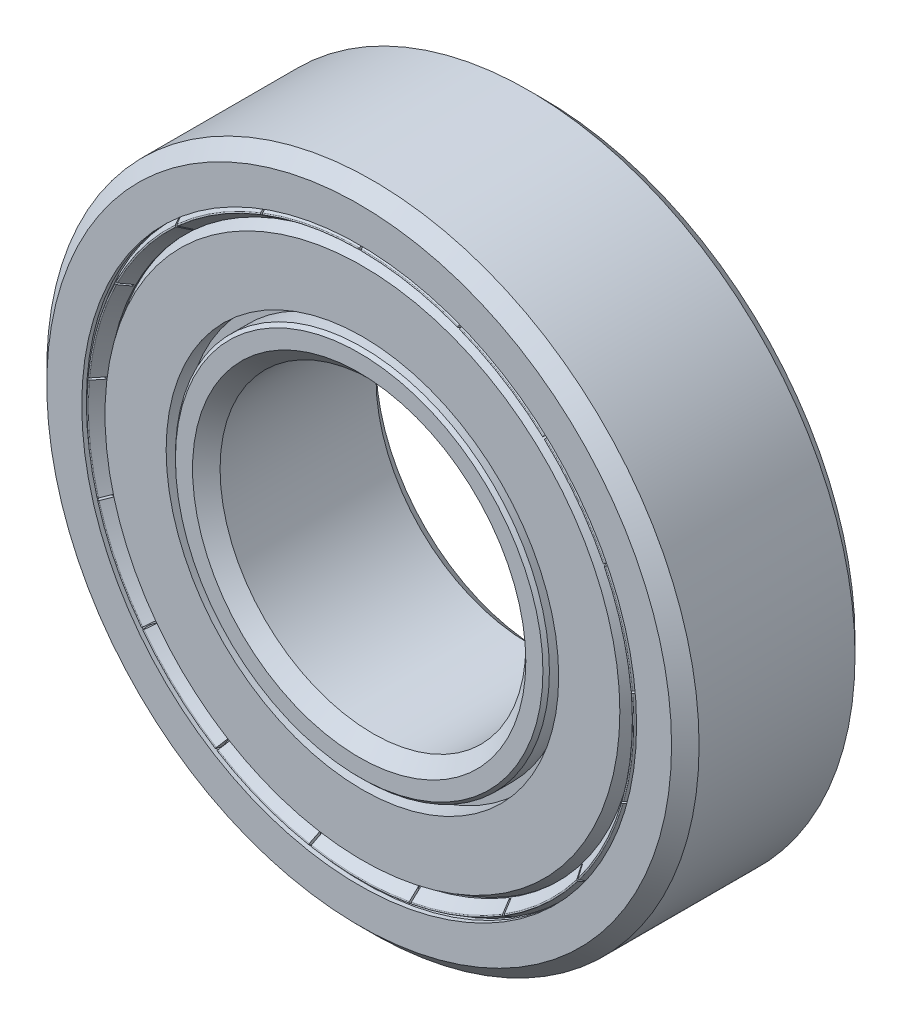
SolidWorks part; units mm, degrees
material "Plain Carbon Steel"
ref_plane "Front Plane" through (0, 0, 0) normal (0, 0, 1) x (1, 0, 0)
ref_plane "Top Plane" through (0, 0, 0) normal (0, 1, 0) x (1, 0, 0)
ref_plane "Right Plane" through (0, 0, 0) normal (1, 0, 0) x (0, 0, -1)
sketch "Sketch1" plane through (0, 0, 0) normal (0, 0, 1) x (1, 0, 0)
  circle A0 centre (0, 0) radius 7.5
  circle A1 centre (0, 0) radius 16
  dimension "OD" = 32
  dimension "ID" = 15
sketch "Sketch2" plane through (0, 0, 0) normal (1, 0, 0) x (0, 0, -1)
  line L0 (-4.5, 16) -> (4.5, 16)
  line L1 (-4.5, 7.5) -> (-4.5, -7.5) construction
  line L2 (4.5, 16) -> (4.5, -16) construction
  line L3 (-4.5, 0) -> (4.5, 0) construction
  line L6 (0, 16) -> (0, 7.5) construction
  circle A0 centre (0, 11.75) radius 2.975 construction
  point P8 (0, 16)
  dimension "Approx. Ball Dia." = 5.95
  dimension "Width" = 9
  dimension "For Shaft Diameter" = 15
  dimension "For Housing ID" = 32
sketch "Sketch3" plane through (0, 0, 0) normal (1, 0, 0) x (0, 0, -1)
  line L0 (0, 0) -> (0, 15) construction
  line L1 (-4.5, 7.5) -> (-4.5, -7.5) construction
  line L2 (3.825, 16) -> (-3.825, 16)
  line L3 (-3.825, 16) -> (-4.5, 15.325)
  line L4 (-4.5, 15.325) -> (-4.5, 13.6097)
  line L5 (-4.5, 13.6097) -> (-4.275, 13.6097)
  line L6 (-4.275, 13.6097) -> (-4.275, 14.1673)
  line L7 (-4.275, 14.1673) -> (-4.1159, 14.3264)
  line L8 (-4.1159, 14.3264) -> (-1.4875, 14.3264)
  line L10 (-4.5, 16) -> (4.5, 16) construction
  line L12 (-4.275, 14.1673) -> (-4.275, 14.725) construction
  line L13 (4.1159, 14.3264) -> (1.4875, 14.3264)
  line L14 (4.275, 14.1673) -> (4.1159, 14.3264)
  line L15 (4.275, 13.6097) -> (4.275, 14.1673)
  line L16 (4.5, 13.6097) -> (4.275, 13.6097)
  line L17 (4.5, 15.325) -> (4.5, 13.6097)
  line L18 (3.825, 16) -> (4.5, 15.325)
  line L19 (3.825, 7.5) -> (-3.825, 7.5)
  line L20 (-3.825, 7.5) -> (-4.5, 8.175)
  line L21 (-4.5, 8.175) -> (-4.5, 9.0145)
  line L22 (-4.5, 9.0145) -> (-4.3409, 9.1736)
  line L23 (-4.3409, 9.1736) -> (-1.4875, 9.1736)
  line L25 (4.3409, 9.1736) -> (1.4875, 9.1736)
  line L26 (4.5, 9.0145) -> (4.3409, 9.1736)
  line L27 (4.5, 8.175) -> (4.5, 9.0145)
  line L28 (3.825, 7.5) -> (4.5, 8.175)
  circle A2 centre (0, 11.75) radius 2.975 construction
  arc A3 (-1.4875, 14.3264) -> (1.4875, 14.3264) centre (0, 11.75) cw
  arc A4 (-1.4875, 9.1736) -> (1.4875, 9.1736) centre (0, 11.75) ccw
  point P5 (0, 14.725)
  point P31 (0, 16)
  point P37 (0, 7.5)
  dimension "D1" = 45
  dimension "D2" = 0.225
  dimension "D3" = 2.975
  dimension "D4" = 0.675
revolve "Revolve1" add sketch "Sketch3" angle 360 about L3
sketch "Sketch4" plane through (0, 0, 0) normal (1, 0, 0) x (0, 0, -1)
  line L0 (0, 14.725) -> (0, 8.775)
  line L1 (0, 16) -> (0, 7.5) construction
  circle A0 centre (0, 11.75) radius 2.975 construction
  arc A1 (0, 8.775) -> (0, 14.725) centre (0, 11.75) cw
revolve "Revolve2" add sketch "Sketch4" angle 360 about L6
pattern_circular "CirPattern1" count 8 over 360 about axis through (0, 0, 0) along (0, 0, 1) of bodies 106
sketch "Sketch5" plane through (0, 0, 0) normal (1, 0, 0) x (0, 0, -1)
  line L0 (-2.975, 11.75) -> (-2.975, 9.1736) construction
  line L1 (-4.3409, 9.1736) -> (-1.4875, 9.1736) construction
  line L3 (-2.975, 9.1736) -> (-3.4303, 9.1736)
  line L4 (-3.4303, 9.1736) -> (-3.4303, 9.6289)
  line L5 (-3.4303, 9.6289) -> (-4.3409, 9.6289)
  line L6 (-4.3409, 9.6289) -> (-4.3409, 12.6286)
  line L7 (-4.3409, 12.6286) -> (-3.4303, 13.1544)
  line L8 (-3.4303, 13.1544) -> (-2.975, 13.1544)
  line L9 (-2.975, 13.1544) -> (-2.975, 9.1736)
  line L10 (0, 11.75) -> (0, 16) construction
  line L11 (3.4303, 13.1544) -> (2.975, 13.1544)
  line L12 (4.3409, 12.6286) -> (3.4303, 13.1544)
  line L13 (4.3409, 9.6289) -> (4.3409, 12.6286)
  line L14 (3.4303, 9.6289) -> (4.3409, 9.6289)
  line L15 (3.4303, 9.1736) -> (3.4303, 9.6289)
  line L16 (2.975, 9.1736) -> (3.4303, 9.1736)
  line L17 (2.975, 13.1544) -> (2.975, 9.1736)
  line L18 (-4.3409, 12.6286) -> (-3.8856, 12.6286) construction
  line L19 (-3.8856, 12.6286) -> (-3.4303, 12.6286) construction
  line L20 (-3.4303, 12.6286) -> (-2.975, 12.6286) construction
  line L21 (-3.4303, 13.1544) -> (-3.4303, 13.6097) construction
  circle A0 centre (0, 11.75) radius 2.975 construction
  dimension "D1" = 30
revolve "Revolve3" add sketch "Sketch5" angle 360 about L3
sketch "Sketch6" plane through (0, 0, 0) normal (1, 0, 0) x (0, 0, -1)
  line L0 (-3.7517, 13.6097) -> (-4.1062, 13.6097)
  line L1 (-4.1062, 13.6097) -> (-4.5, 13.3823)
  line L2 (-4.5, 13.3823) -> (-3.8867, 12.9529)
  line L4 (-4.3409, 12.6286) -> (-3.4303, 13.1544) construction
  line L5 (-3.7517, 12.9688) -> (-3.7517, 13.6097)
  line L6 (-4.5, 13.6097) -> (-4.275, 13.6097) construction
  line L7 (-3.8867, 12.9529) -> (-3.8417, 12.9529)
  line L8 (-3.8417, 12.9529) -> (-3.7517, 12.9688)
  line L9 (-4.5, 15.325) -> (-4.5, -15.325) construction
  line L11 (-3.8417, 12.9529) -> (-3.7967, 12.9529) construction
  line L12 (-3.7967, 12.9529) -> (-3.7517, 12.9529) construction
  point P27 (-3.929, 13.6097)
  dimension "D1" = 30
  dimension "D3" = 10
  dimension "D2" = 35
  dimension "D4" = 0.045
  dimension "D5" = 0.3937
revolve "Revolve4" add sketch "Sketch6" angle 360 about L3
fillet "Fillet1" radius 0.045 1 edges at (13.3823, 0, 4.5)
sketch "Sketch7" plane through (0, 0, 0) normal (0, 0, 1) x (1, 0, 0)
  line L0 (-0.05, 13.6097) -> (-0.05, 13.7097)
  line L1 (-0.05, 13.6097) -> (0.05, 13.6097) construction
  line L2 (-0.05, 13.6097) -> (-0.05, 12.9529)
  line L3 (-0.05, 12.9529) -> (0.05, 12.9529) construction
  line L4 (0.05, 13.6097) -> (0.05, 12.9529)
  line L5 (-0.05, 13.7097) -> (0.05, 13.7097)
  line L6 (0.05, 13.7097) -> (0.05, 13.6097)
  line L7 (-0.05, 12.9529) -> (-0.05, 12.8529)
  line L8 (-0.05, 12.8529) -> (0.05, 12.8529)
  line L9 (0.05, 12.8529) -> (0.05, 12.9529)
  dimension "D1" = 0.1
extrude "Cut-Extrude1" cut sketch "Sketch7" along normal through all from vertex at 3.929 starting at point (0, 13.6097, 3.929)
pattern_circular "CirPattern2" count 17 over 360 about axis through (0, 0, 0) along (0, 0, 1) of "Cut-Extrude1"
mirror "Mirror1" about plane through (0, 0, 0) normal (0, 0, 1) of bodies 120
equation "\"Approx. Ball Dia.@Sketch2\"=( \"OD@Sketch1\" - \"ID@Sketch1\" )  * .5 * .7"
equation "\"D2@Sketch3\"=\"Width@Sketch2\"*.025"
equation "\"D3@Sketch3\"=\"Approx. Ball Dia.@Sketch2\"*.5"
equation "\"D4@Sketch3\"=\"Width@Sketch2\"*.075"
equation "\"Approx No of Balls\"= ( pi * \"OD@Sketch1\" ) * .5 / \"Approx. Ball Dia.@Sketch2\""
equation "\"D1@CirPattern1\"=\"Approx No of Balls\""
equation "\"D4@Sketch6\"=\"D2@Sketch3\"*.2"
equation "\"D1@CirPattern2\"=\"Approx No of Balls\"*2"
equation "\"D5@Sketch6\"=\"D2@Sketch3\"*1.75"
equation "\"D1@Fillet1\"=\"d4@sketch6\""
